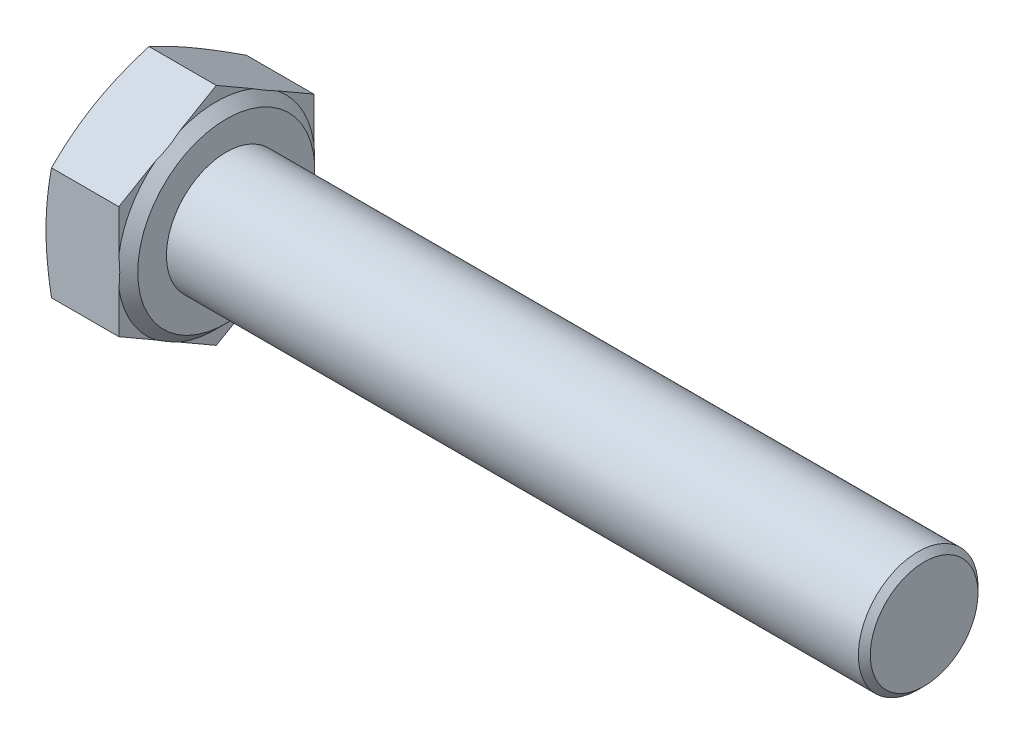
SolidWorks part; units mm, degrees
ref_plane "Front" through (0, 0, 0) normal (0, 0, 1) x (1, 0, 0)
ref_plane "Top" through (0, 0, 0) normal (0, 1, 0) x (1, 0, 0)
ref_plane "Right" through (0, 0, 0) normal (1, 0, 0) x (0, 0, -1)
sketch "Sketch2" plane through (0, 0, 0) normal (1, 0, 0) x (0, 0, -1)
  line L1 (4.89, -2.8232) -> (4.89, 2.8232)
  line L2 (4.89, 2.8232) -> (0, 5.6465)
  line L3 (0, 5.6465) -> (-4.89, 2.8232)
  line L4 (-4.89, 2.8232) -> (-4.89, -2.8232)
  line L5 (-4.89, -2.8232) -> (0, -5.6465)
  line L6 (0, -5.6465) -> (4.89, -2.8232)
  circle A0 centre (0, 0) radius 4.89 construction
  dimension "s" = 9.78
extrude "BaseHead" add sketch "Sketch2" along normal blind 4.15
sketch "Sketch3" plane through (0, 0, 0) normal (0, 0, 1) x (1, 0, 0)
  line L0 (4.15, 5.6465) -> (4.15, 4.44)
  line L2 (4.15, 4.44) -> (3.65, 4.94)
  line L3 (3.65, 4.94) -> (3.65, 5.6465)
  line L5 (3.65, 5.6465) -> (4.15, 5.6465)
  line L6 (-0.9571, 0) -> (7.6478, 0) construction
  line L7 (4.15, 5.6465) -> (0, 5.6465) construction
  dimension "D1" = 45
  dimension "c" = 0.5
  dimension "Dw" = 8.88
revolve "BearingFace" cut sketch "Sketch3" angle 360 about L6
sketch "Sketch4" plane through (0, 0, 0) normal (0, 0, 1) x (1, 0, 0)
  line L0 (-0.4935, 0) -> (3.5626, 0) construction
  line L2 (0, 5.6465) -> (0.2753, 5.6465)
  line L4 (0.2753, 5.6465) -> (0, 4.89)
  line L6 (0, 4.89) -> (0, 5.6465)
  line L7 (3.65, 5.6465) -> (0, 5.6465) construction
  dimension "D1" = 20
  dimension "D2" = 9.78
revolve "HeadChamfer" cut sketch "Sketch4" angle 360 about L0
sketch "Sketch5" plane through (4.15, 0, 0) normal (1, 0, 0) x (0, 0, -1)
  circle A0 centre (0, 0) radius 3
  dimension "d" = 6
extrude "BaseBody" add sketch "Sketch5" along normal blind 35
cosmetic thread "ThreadCosmetic1" [suppressed] parameters "D2"=4.917
chamfer "Chamfer1" distance 0.3 angle 45 1 edges at (39.15, 0, -3)
fillet "HeadFillet" [suppressed] radius 0.25
sketch "Sketch6" plane through (0, 0, 0) normal (0, 0, 1) x (1, 0, 0)
  line L0 (4.15, 3.5415) -> (4.6915, 3.5415)
  line L1 (4.6915, 3.5415) -> (4.6915, 3)
  line L2 (4.6915, 3) -> (4.4208, 2.531)
  line L3 (4.4208, 2.531) -> (4.15, 3)
  line L4 (4.15, 3) -> (4.15, 3.5415)
  line L5 (38.85, 3) -> (4.15, 3) construction
  line L6 (4.15, -4.44) -> (4.15, 4.44) construction
  dimension "D1" = 0.5415
revolve "Cut-Revolve10" [suppressed] cut sketch "Sketch6" angle 360 about axis through (-0.9571, 0, 0) along (1, 0, 0)
pattern_linear "LPattern10" [suppressed] count 54
equation "\"D2@Sketch4\" = \"s@Sketch2\""
equation "\"D1@Chamfer1\" = 0.05 * \"d@Sketch5\""
equation "\"D1@Sketch6\" =  ( \"d@Sketch5\" - \"D2@ThreadCosmetic1\" )  / 2"
equation "\"pitch@LPattern10\" = \"D1@Sketch6\" * 1.2"
equation "\"D1@LPattern10\" = \"l@BaseBody\" / \"pitch@LPattern10\""
